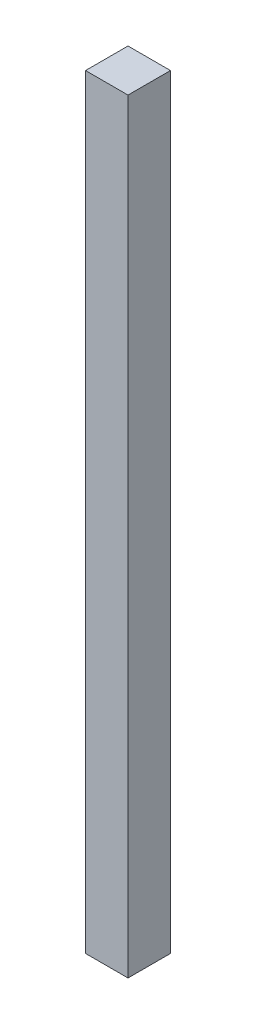
SolidWorks part; units mm, degrees
ref_plane "Front Plane" through (0, 0, 0) normal (0, 0, 1) x (1, 0, 0)
ref_plane "Top Plane" through (0, 0, 0) normal (0, 1, 0) x (1, 0, 0)
ref_plane "Right Plane" through (0, 0, 0) normal (1, 0, 0) x (0, 0, -1)
sketch "Sketch1" plane through (0, 0, 0) normal (0, 1, 0) x (1, 0, 0)
  line L1 (0, 0) -> (38.1, 0)
  line L2 (0, 0) -> (0, -38.1)
  line L3 (0, -38.1) -> (38.1, -38.1)
  line L4 (38.1, 0) -> (38.1, -38.1)
extrude "Boss-Extrude1" add sketch "Sketch1" along normal blind 685.8
